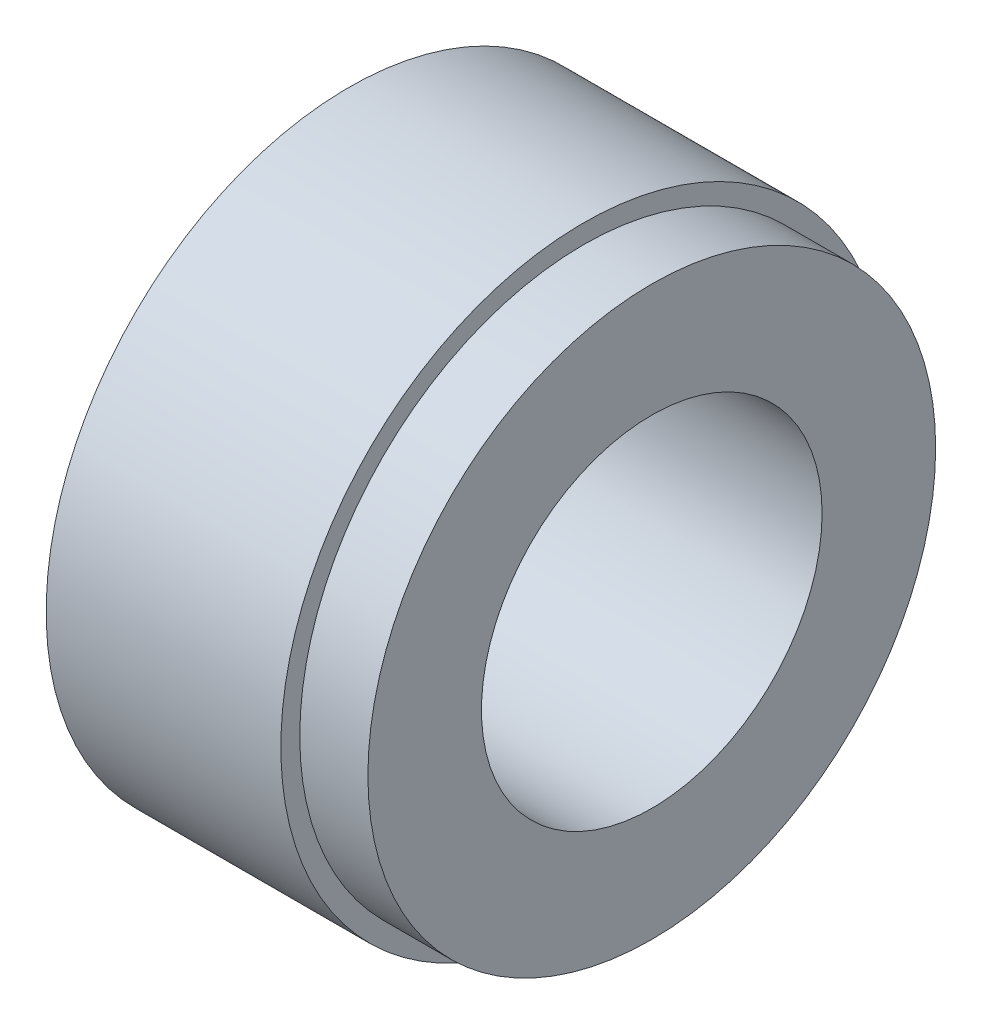
SolidWorks part; units mm, degrees
ref_plane "Front" through (0, 0, 0) normal (0, 0, 1) x (1, 0, 0)
ref_plane "Top" through (0, 0, 0) normal (0, 1, 0) x (1, 0, 0)
ref_plane "Right" through (0, 0, 0) normal (1, 0, 0) x (0, 0, -1)
sketch "Sketch1" plane through (0, 0, 0) normal (0, 0, 1) x (1, 0, 0)
  line L0 (0, 4.5) -> (0, 7.5)
  line L1 (0, 7.5) -> (-1.8, 7.5)
  line L2 (-1.8, 7.5) -> (-1.8, 8)
  line L3 (-1.8, 8) -> (-8, 8)
  line L4 (-8, 8) -> (-8, 4.5)
  line L5 (-8, 4.5) -> (0, 4.5)
  line L6 (0, 0) -> (-25.8192, 0) construction
  dimension "D1" = 4.5
  dimension "D2" = 7.5
  dimension "D3" = 8
  dimension "D4" = 8
  dimension "D5" = 6.2
revolve "Base-Revolve" add sketch "Sketch1" angle 360 about L6
